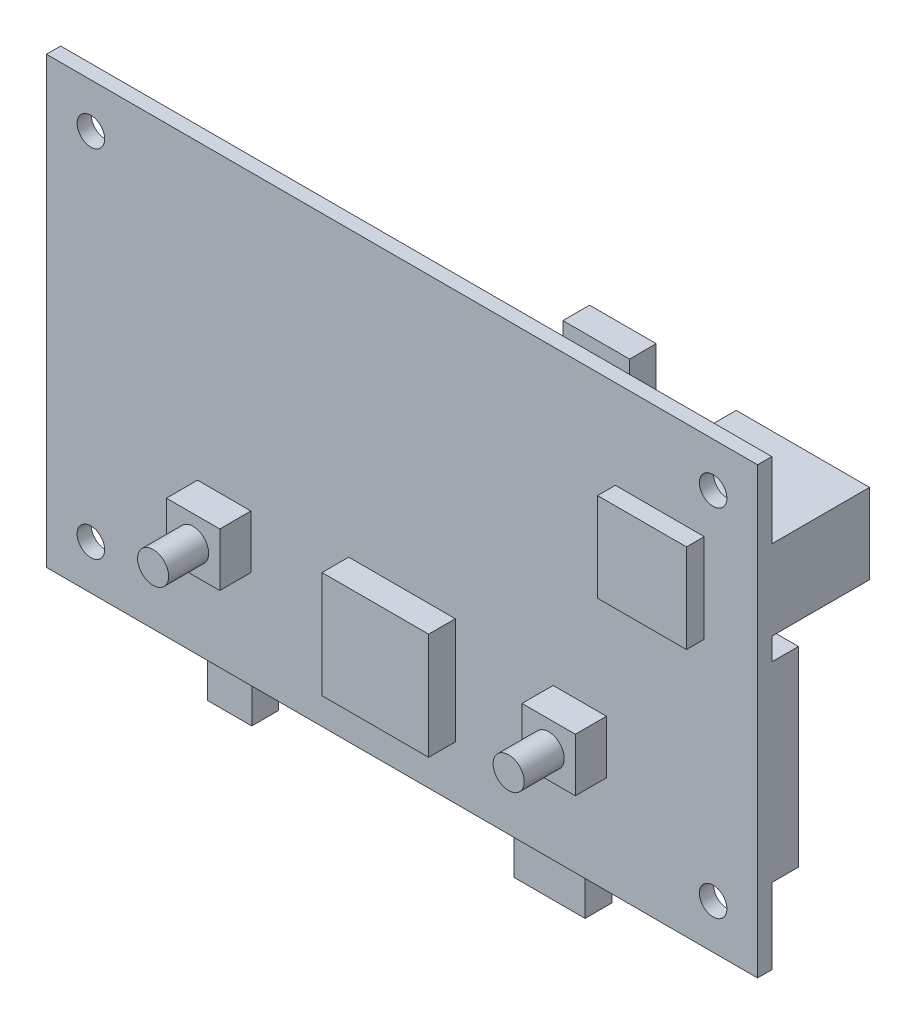
SolidWorks part; units mm, degrees
ref_plane "正面" through (0, 0, 0) normal (0, 0, 1) x (1, 0, 0)
ref_plane "平面" through (0, 0, 0) normal (0, 1, 0) x (1, 0, 0)
ref_plane "右側面" through (0, 0, 0) normal (1, 0, 0) x (0, 0, -1)
sketch "ｽｹｯﾁ1" plane through (0, 0, 0) normal (0, 0, 1) x (1, 0, 0)
  line L1 (0, 0) -> (80, 0)
  line L2 (0, 0) -> (0, 50)
  line L3 (0, 50) -> (80, 50)
  line L4 (80, 0) -> (80, 50)
  dimension "D1" = 80
  dimension "D2" = 50
extrude "ﾎﾞｽ - 押し出し1" add sketch "ｽｹｯﾁ1" along normal blind 1.6
sketch "ｽｹｯﾁ2" plane through (0, 0, 1.6) normal (0, 0, 1) x (1, 0, 0)
  line L0 (0, 25) -> (80, 25) construction
  line L1 (0, 50) -> (0, 0) construction
  line L2 (80, 0) -> (80, 50) construction
  line L3 (40, 50) -> (40, 0) construction
  line L4 (80, 50) -> (0, 50) construction
  line L5 (0, 0) -> (80, 0) construction
  circle A1 centre (75, 45) radius 1.55
  circle A3 centre (75, 5) radius 1.55
  circle A4 centre (5, 5) radius 1.55
  circle A5 centre (5, 45) radius 1.55
  dimension "D2" = 3.1
  dimension "D3" = 3.1
  dimension "D5" = 5
  dimension "D6" = 5
  dimension "D7" = 5
  dimension "D8" = 5
extrude "ｶｯﾄ - 押し出し1" cut sketch "ｽｹｯﾁ2" against normal through all
sketch "ｽｹｯﾁ3" plane through (0, 0, 1.6) normal (0, 0, 1) x (1, 0, 0)
  line L0 (80, 0) -> (80, 50) construction
  line L5 (57, 17) -> (63, 17)
  line L6 (57, 17) -> (57, 11)
  line L7 (57, 11) -> (63, 11)
  line L8 (63, 17) -> (63, 11)
  line L9 (17, 17) -> (23, 17)
  line L10 (17, 17) -> (17, 11)
  line L11 (17, 11) -> (23, 11)
  line L12 (23, 17) -> (23, 11)
  line L21 (0, 0) -> (80, 0) construction
  line L22 (0, 50) -> (0, 0) construction
  dimension "D1" = 6
  dimension "D2" = 6
  dimension "D3" = 6
  dimension "D4" = 6
  dimension "D5" = 17
  dimension "D6" = 11
  dimension "D7" = 11
  dimension "D8" = 17
extrude "ﾎﾞｽ - 押し出し2" add sketch "ｽｹｯﾁ3" along normal blind 3.5
sketch "ｽｹｯﾁ4" plane through (0, 0, 5.1) normal (0, 0, 1) x (1, 0, 0)
  line L0 (17, 14) -> (23, 14) construction
  line L1 (17, 17) -> (17, 11) construction
  line L2 (23, 11) -> (23, 17) construction
  line L3 (20, 17) -> (20, 11) construction
  line L4 (23, 17) -> (17, 17) construction
  line L5 (17, 11) -> (23, 11) construction
  line L6 (60, 17) -> (60, 11) construction
  line L7 (63, 17) -> (57, 17) construction
  line L8 (57, 11) -> (63, 11) construction
  line L9 (63, 14) -> (57, 14) construction
  line L10 (63, 11) -> (63, 17) construction
  circle A0 centre (20, 14) radius 1.75
  circle A1 centre (60, 14) radius 1.75
  dimension "D1" = 3.5
  dimension "D2" = 3.5
extrude "ﾎﾞｽ - 押し出し3" add sketch "ｽｹｯﾁ4" along normal blind 4.5
sketch "ｽｹｯﾁ5" plane through (0, 0, 1.6) normal (0, 0, 1) x (1, 0, 0)
  line L0 (40, 50) -> (40, 0) construction
  line L1 (34, 18) -> (46, 18)
  line L2 (34, 18) -> (34, 6)
  line L3 (34, 6) -> (46, 6)
  line L4 (46, 18) -> (46, 6)
  line L6 (80, 50) -> (0, 50) construction
  line L7 (0, 0) -> (80, 0) construction
  line L8 (40, 18) -> (40, 6) construction
  dimension "D1" = 12
  dimension "D2" = 12
  dimension "D3" = 6
extrude "ﾎﾞｽ - 押し出し4" add sketch "ｽｹｯﾁ5" along normal blind 3
sketch "ｽｹｯﾁ6" plane through (0, 0, 1.6) normal (0, 0, 1) x (1, 0, 0)
  line L0 (80, 0) -> (80, 50) construction
  line L1 (64, 40) -> (74, 40)
  line L2 (64, 40) -> (64, 30)
  line L3 (64, 30) -> (74, 30)
  line L4 (74, 40) -> (74, 30)
  line L5 (80, 50) -> (0, 50) construction
  dimension "D1" = 10
  dimension "D2" = 10
  dimension "D3" = 6
  dimension "D4" = 10
extrude "ﾎﾞｽ - 押し出し5" add sketch "ｽｹｯﾁ6" along normal blind 2
sketch "ｽｹｯﾁ7" plane through (0, 0, 0) normal (0, 0, -1) x (-1, 0, 0)
  line L0 (0, 50) -> (0, 0) construction
  line L1 (-29, 43) -> (-13, 43)
  line L2 (-29, 43) -> (-29, 25)
  line L3 (-29, 25) -> (-13, 25)
  line L4 (-13, 43) -> (-13, 25)
  line L5 (-6.5, 29) -> (-3.5, 29)
  line L6 (-6.5, 29) -> (-6.5, 25)
  line L7 (-6.5, 25) -> (-3.5, 25)
  line L8 (-3.5, 29) -> (-3.5, 25)
  line L9 (-21.5, 5) -> (-16.5, 5)
  line L10 (-21.5, 5) -> (-21.5, -5.5)
  line L11 (-21.5, -5.5) -> (-16.5, -5.5)
  line L12 (-16.5, 5) -> (-16.5, -5.5)
  line L13 (-59, 5) -> (-51, 5)
  line L14 (-59, 5) -> (-59, -5.5)
  line L15 (-59, -5.5) -> (-51, -5.5)
  line L16 (-51, 5) -> (-51, -5.5)
  line L17 (-69.5, 30) -> (-80, 30)
  line L18 (-69.5, 30) -> (-69.5, 8.5)
  line L19 (-69.5, 8.5) -> (-80, 8.5)
  line L20 (-80, 30) -> (-80, 8.5)
  line L21 (-64, 51.5) -> (-56.5, 51.5)
  line L22 (-64, 51.5) -> (-64, 44.5)
  line L23 (-64, 44.5) -> (-56.5, 44.5)
  line L24 (-56.5, 51.5) -> (-56.5, 44.5)
  line L25 (-52.2, 44.5) -> (-43.2, 44.5)
  line L26 (-52.2, 44.5) -> (-52.2, 39.5)
  line L27 (-52.2, 39.5) -> (-43.2, 39.5)
  line L28 (-43.2, 44.5) -> (-43.2, 39.5)
  line L29 (-42, 41) -> (-38, 41)
  line L30 (-42, 41) -> (-42, 38)
  line L31 (-42, 38) -> (-38, 38)
  line L32 (-38, 41) -> (-38, 38)
  line L33 (-63.5, 29) -> (-58.5, 29)
  line L34 (-63.5, 29) -> (-63.5, 25)
  line L35 (-63.5, 25) -> (-58.5, 25)
  line L36 (-58.5, 29) -> (-58.5, 25)
  line L37 (-80, 50) -> (0, 50) construction
  line L38 (0, 0) -> (-80, 0) construction
  line L39 (-80, 0) -> (-80, 50) construction
  dimension "D1" = 3.5
  dimension "D2" = 21
  dimension "D3" = 3
  dimension "D4" = 4
  dimension "D5" = 18
  dimension "D6" = 16
  dimension "D7" = 13
  dimension "D8" = 25
  dimension "D9" = 16
  dimension "D10" = 5.5
  dimension "D11" = 7.5
  dimension "D12" = 7
  dimension "D13" = 9
  dimension "D14" = 5
  dimension "D15" = 5.5
  dimension "D16" = 27.8
  dimension "D17" = 3
  dimension "D18" = 4
  dimension "D19" = 9
  dimension "D20" = 38
  dimension "D21" = 4
  dimension "D22" = 5
  dimension "D23" = 21
  dimension "D24" = 16.5
  dimension "D25" = 10.5
  dimension "D26" = 21.5
  dimension "D27" = 10.5
  dimension "D28" = 8.5
  dimension "D29" = 8
  dimension "D30" = 10.5
  dimension "D31" = 5.5
  dimension "D32" = 21
  dimension "D33" = 5
  dimension "D34" = 10.5
  dimension "D35" = 5.5
  dimension "D36" = 16.5
extrude "ﾎﾞｽ - 押し出し6" add sketch "ｽｹｯﾁ7" along normal blind 3
sketch "ｽｹｯﾁ8" plane through (0, 0, 0) normal (0, 0, -1) x (-1, 0, 0)
  line L0 (-56.5, 50) -> (0, 50) construction
  line L1 (-43.1, 34.5) -> (-36.6, 34.5)
  line L2 (-43.1, 34.5) -> (-43.1, 26.5)
  line L3 (-43.1, 26.5) -> (-36.6, 26.5)
  line L4 (-36.6, 34.5) -> (-36.6, 26.5)
  line L5 (0, 50) -> (0, 0) construction
  dimension "D1" = 6.5
  dimension "D2" = 8
  dimension "D3" = 15.5
  dimension "D4" = 36.6
extrude "ﾎﾞｽ - 押し出し7" add sketch "ｽｹｯﾁ8" along normal blind 5
sketch "ｽｹｯﾁ9" plane through (0, 0, 0) normal (0, 0, -1) x (-1, 0, 0)
  line L0 (-80, 30) -> (-80, 50) construction
  line L2 (-80, 41.5) -> (-65, 41.5)
  line L3 (-80, 41.5) -> (-80, 32.5)
  line L4 (-80, 32.5) -> (-65, 32.5)
  line L5 (-65, 41.5) -> (-65, 32.5)
  line L6 (-80, 50) -> (-64, 50) construction
  dimension "D1" = 9
  dimension "D2" = 15
  dimension "D3" = 8.5
extrude "ﾎﾞｽ - 押し出し8" add sketch "ｽｹｯﾁ9" along normal blind 11
